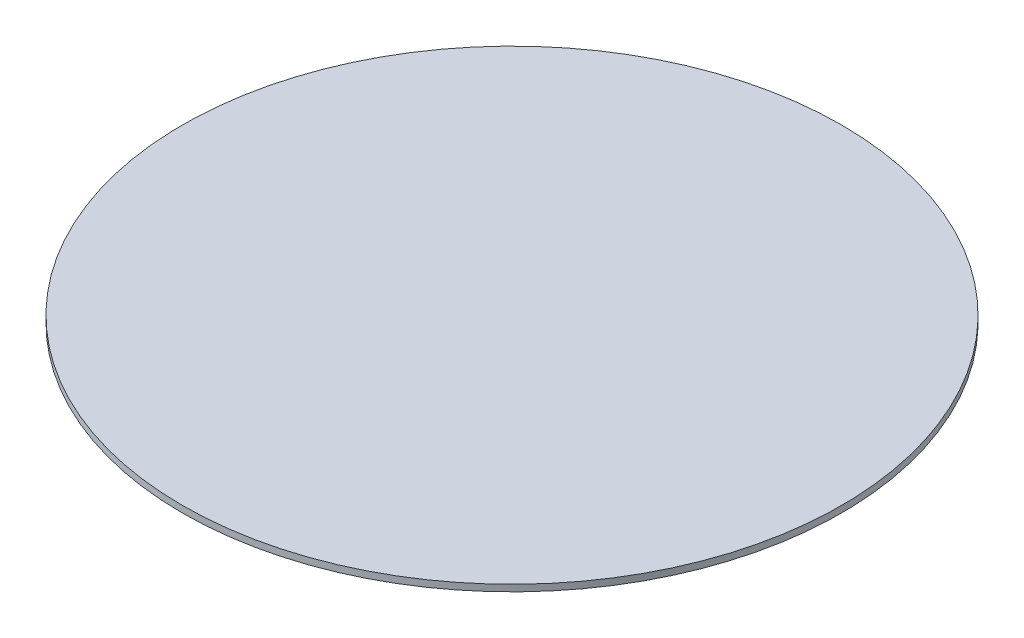
SolidWorks part; units mm, degrees
ref_plane "Front Plane" through (0, 0, 0) normal (0, 0, 1) x (1, 0, 0)
ref_plane "Top Plane" through (0, 0, 0) normal (0, 1, 0) x (1, 0, 0)
ref_plane "Right Plane" through (0, 0, 0) normal (1, 0, 0) x (0, 0, -1)
sketch "Sketch1" plane through (0, 0, 0) normal (0, 1, 0) x (1, 0, 0)
  circle A0 centre (0, 0) radius 25
  dimension "D1" = 50
extrude "Boss-Extrude1" add sketch "Sketch1" along normal blind 0.5
